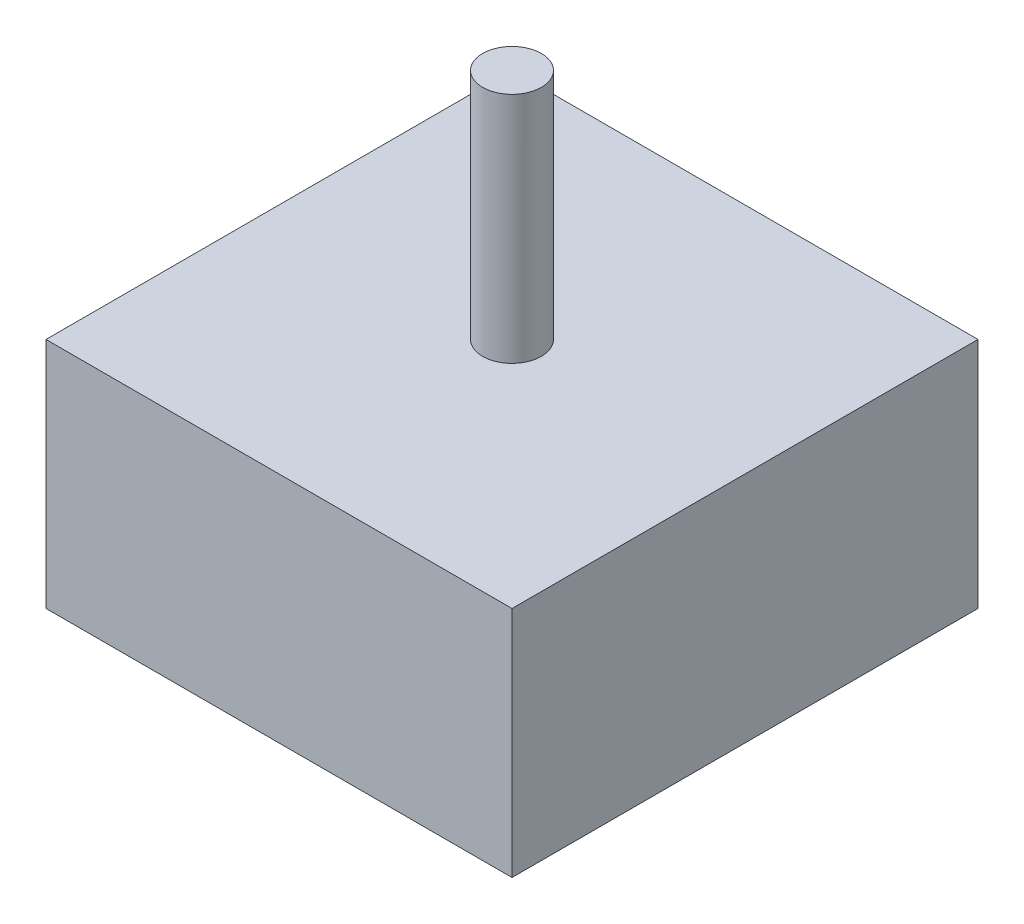
SolidWorks part; units mm, degrees
ref_plane "Front Plane" through (0, 0, 0) normal (0, 0, 1) x (1, 0, 0)
ref_plane "Top Plane" through (0, 0, 0) normal (0, 1, 0) x (1, 0, 0)
ref_plane "Right Plane" through (0, 0, 0) normal (1, 0, 0) x (0, 0, -1)
sketch "Sketch1" plane through (0, 0, 0) normal (0, 1, 0) x (1, 0, 0)
  line L1 (-25, -25) -> (25, -25)
  line L2 (-25, -25) -> (-25, 25)
  line L3 (-25, 25) -> (25, 25)
  line L4 (25, -25) -> (25, 25)
  line L5 (-25, -25) -> (25, 25) construction
  line L6 (-25, 25) -> (25, -25) construction
  point P0 (0, 0)
extrude "Boss-Extrude1" add sketch "Sketch1" along normal blind 25
sketch "Sketch2" plane through (0, 25, 0) normal (0, 1, 0) x (1, 0, 0)
  circle A0 centre (0, 0) radius 3.15
extrude "Boss-Extrude2" add sketch "Sketch2" along normal blind 25
sketch "Sketch3" plane through (-25, 0, 0) normal (-1, 0, 0) x (0, 0, 1)
  line L0 (-25, 25) -> (25, 0) construction
  line L1 (-25, 0) -> (25, 25) construction
  line L3 (-2.5, 10) -> (2.5, 10)
  line L4 (-2.5, 10) -> (-2.5, 15)
  line L5 (-2.5, 15) -> (2.5, 15)
  line L6 (2.5, 10) -> (2.5, 15)
  line L7 (-2.5, 10) -> (2.5, 15) construction
  line L8 (-2.5, 15) -> (2.5, 10) construction
  point P8 (0, 12.5)
extrude "Cut-Extrude2" cut sketch "Sketch3" against normal blind 6
